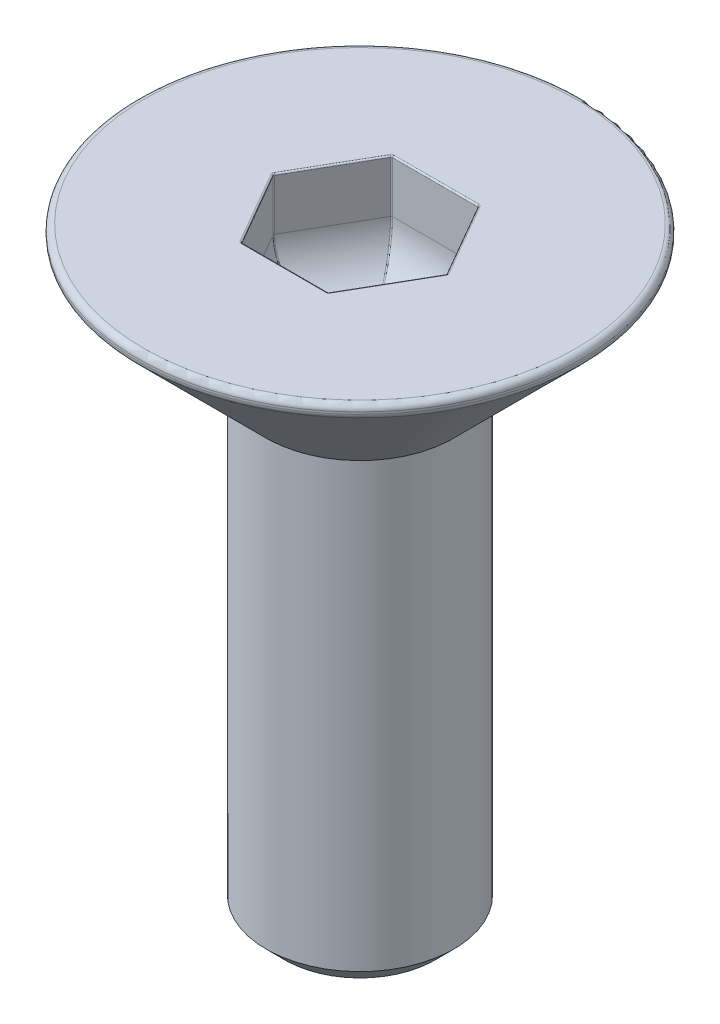
SolidWorks part; units mm, degrees
ref_plane "Front" through (0, 0, 0) normal (0, 0, 1) x (1, 0, 0)
ref_plane "Top" through (0, 0, 0) normal (0, 1, 0) x (1, 0, 0)
ref_plane "Right" through (0, 0, 0) normal (1, 0, 0) x (0, 0, -1)
sketch "Sketch8" plane through (0, 0, 0) normal (0, 0, 1) x (1, 0, 0)
  line L1 (0, 0) -> (1.25, 0)
  line L2 (0, 0) -> (0, -8)
  line L3 (0, -8) -> (1.25, -8)
  line L4 (1.25, 0) -> (1.25, -8)
  dimension "D1" = 8
revolve "Revolve1" add sketch "Sketch8" angle 360 about L2
chamfer "Chamfer1" distance 0.25 angle 45 1 edges at (-1.25, -8, 0)
sketch "Sketch9" plane through (0, 0, 0) normal (0, 1, 0) x (1, 0, 0)
  circle A0 centre (0, 0) radius 1.5
thread "Thread2" pitch 0.5 start angle 0, offset 0, length 15, pitch 0.5, diameter 3
ref_plane "Plane2" through (-1.5, 0, 0) normal (0, 0, -1) x (1, 0, 0)
sketch "Thread Profile2" plane through (-1.5, 0, 0) normal (0, 0, -1) x (1, 0, 0)
  line L0 (0, 0) -> (0, 0.5) construction
  line L11 (0, 0.4375) -> (0, 0)
  line L12 (0, 0) -> (0.2706, 0.1563)
  line L13 (0.2706, 0.1563) -> (0.2706, 0.2813)
  line L15 (0.2706, 0.2813) -> (0, 0.4375)
  line L17 (0.2706, 0.2188) -> (0, 0.2188) construction
  point P3 (0, 0)
  dimension "Pitch" = 0.5
  dimension "Profile_Angle" = 60
  dimension "Profile_Land" = 0.125
  dimension "Profile_Height" = 0.2706
sketch "Sketch13" plane through (0, 0, 0) normal (0, 0, 1) x (1, 0, 0)
  line L0 (0, 0) -> (3.1, 0)
  line L1 (0, 0) -> (0, -3.1)
  line L2 (0, -3.1) -> (3.1, 0)
  line L3 (1.55, 0) -> (1.55, -1.55) construction
revolve "Revolve2" add sketch "Sketch13" angle 360 about L1
chamfer "Chamfer2" distance 0.2 angle 45 1 edges at (-3.1, 0, 0)
fillet "Fillet1" radius 0.08 2 edges at (2.9586, 0, 0) (2.9586, -0.1414, 0)
sketch "Sketch14" plane through (0, 0, 0) normal (0, 1, 0) x (1, 0, 0)
  line L1 (1.1547, 0) -> (0.5774, 1)
  line L2 (0.5774, 1) -> (-0.5774, 1)
  line L3 (-0.5774, 1) -> (-1.1547, 0)
  line L4 (-1.1547, 0) -> (-0.5774, -1)
  line L5 (-0.5774, -1) -> (0.5774, -1)
  line L6 (0.5774, -1) -> (1.1547, 0)
  circle A0 centre (0, 0) radius 1 construction
extrude "Cut-Extrude1" cut sketch "Sketch14" against normal blind 1.5
fillet "Fillet2" radius 0.8 6 edges at (0, -1.5, 1) (-0.866, -1.5, 0.5) (-0.866, -1.5, -0.5) (0, -1.5, -1) (0.866, -1.5, -0.5) (0.866, -1.5, 0.5)
fillet "Fillet5" radius 0.02 18 edges at (0, 0, -1) (-0.866, 0, -0.5) (-0.866, 0, 0.5) (0, 0, 1) (0.866, 0, 0.5) (0.866, 0, -0.5) (-0.8841, -1.2657, 0) (-0.4421, -1.2657, 0.7657) (0.4421, -1.2657, 0.7657) (0.8841, -1.2657, 0) (0.4421, -1.2657, -0.7657) (-0.4421, -1.2657, -0.7657) (-1.1547, -0.35, 0) (-0.5774, -0.35, 1) (0.5774, -0.35, 1) (1.1547, -0.35, 0) (0.5774, -0.35, -1) (-0.5774, -0.35, -1)
equation "\"length\"= 8"
equation "\"D1@Sketch8\"=\"length\""
